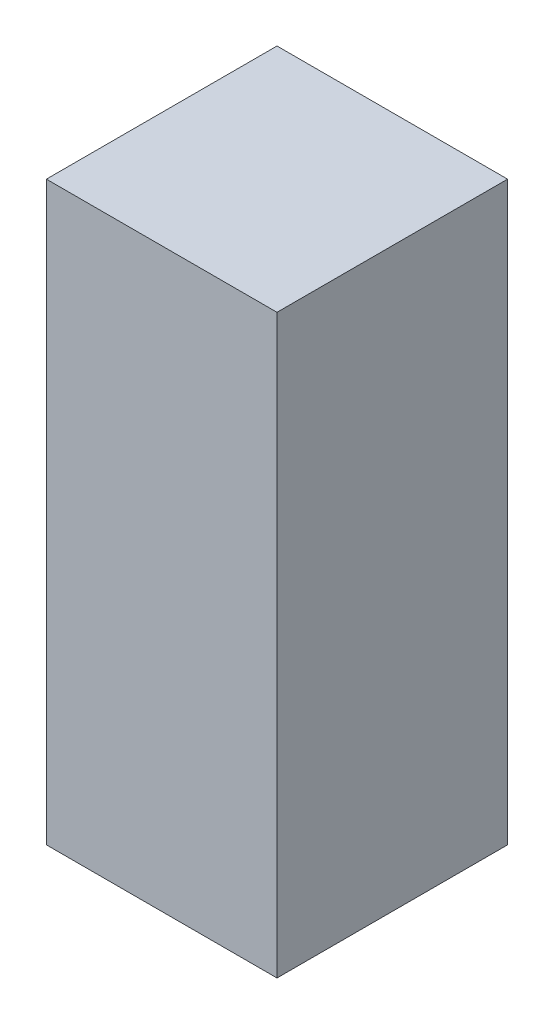
SolidWorks part; units mm, degrees
ref_plane "Front Plane" through (0, 0, 0) normal (0, 0, 1) x (1, 0, 0)
ref_plane "Top Plane" through (0, 0, 0) normal (0, 1, 0) x (1, 0, 0)
ref_plane "Right Plane" through (0, 0, 0) normal (1, 0, 0) x (0, 0, -1)
sketch "Sketch1" plane through (0, 0, 0) normal (0, 1, 0) x (1, 0, 0)
  line L1 (0, 0) -> (20.32, 0)
  line L2 (0, 0) -> (0, 20.32)
  line L3 (0, 20.32) -> (20.32, 20.32)
  line L4 (20.32, 0) -> (20.32, 20.32)
  dimension "D1" = 20.32
  dimension "D2" = 20.32
extrude "Boss-Extrude1" add sketch "Sketch1" along normal blind 50.8
